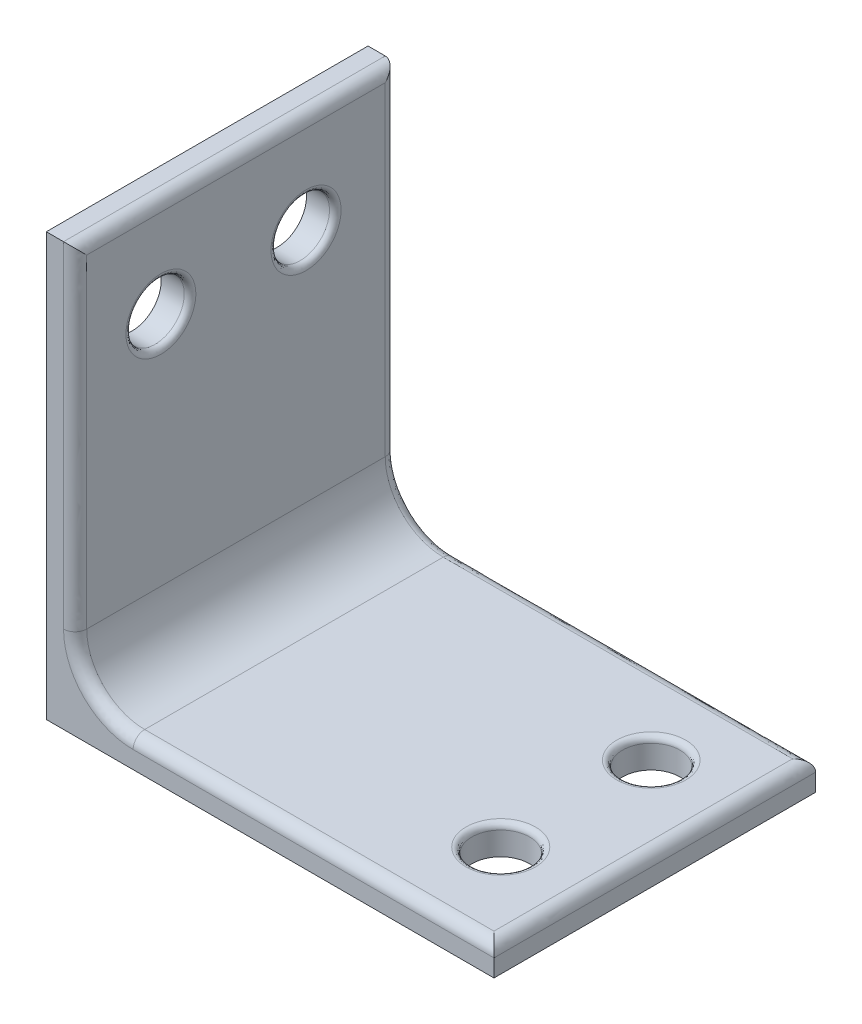
SolidWorks part; units mm, degrees
ref_plane "Front Plane" through (0, 0, 0) normal (0, 0, 1) x (1, 0, 0)
ref_plane "Top Plane" through (0, 0, 0) normal (0, 1, 0) x (1, 0, 0)
ref_plane "Right Plane" through (0, 0, 0) normal (1, 0, 0) x (0, 0, -1)
sketch "Sketch1" plane through (0, 0, 0) normal (0, 1, 0) x (1, 0, 0)
  line L1 (0, 0) -> (77.2022, 0)
  line L2 (0, 0) -> (0, 55.4817)
  line L3 (0, 55.4817) -> (77.2022, 55.4817)
  line L4 (77.2022, 0) -> (77.2022, 55.4817)
extrude "Boss-Extrude1" add sketch "Sketch1" along normal blind 5
sketch "Sketch2" plane through (0, 5, 0) normal (0, 1, 0) x (1, 0, 0)
  line L0 (0, 0) -> (77.2022, 0) construction
  line L1 (0, 55.4817) -> (4.9689, 55.4817)
  line L2 (0, 55.4817) -> (0, 0)
  line L3 (0, 0) -> (4.9689, 0)
  line L4 (4.9689, 55.4817) -> (4.9689, 0)
extrude "Boss-Extrude2" add sketch "Sketch2" along normal blind 67.858
sketch "Sketch3" plane through (0, 5, 0) normal (0, 1, 0) x (1, 0, 0)
  circle A0 centre (63.2119, 41.1146) radius 4.9578
  circle A1 centre (63.2119, 15.1584) radius 4.9805
  point P4 (63.2119, 15.1584)
extrude "Cut-Extrude1" cut sketch "Sketch3" against normal blind 67.858
sketch "Sketch4" plane through (4.9689, 0, 0) normal (1, 0, 0) x (0, 0, -1)
  circle A0 centre (14.7902, 55.6617) radius 5.0256
  circle A1 centre (39.8217, 55.6617) radius 5.0405
  point P4 (14.7902, 55.6617)
extrude "Cut-Extrude2" cut sketch "Sketch4" against normal blind 67.858
fillet "Fillet1" radius 10 1 edges at (4.9689, 5, -27.7408)
fillet "Fillet2" radius 2 8 edges at (4.9689, 72.858, -27.7408) (4.9689, 43.929, -55.4817) (7.1602, 8.7531, -55.4817) (46.0855, 5, -55.4817) (77.2022, 5, -27.7408) (46.0855, 5, 0) (8.722, 7.1913, 0) (4.9689, 43.929, 0)
fillet "Fillet3" radius 1 4 edges at (4.9689, 55.6617, -19.8158) (4.9689, 55.6617, -44.8622) (63.2119, 5, -36.1568) (63.2119, 5, -10.178)
